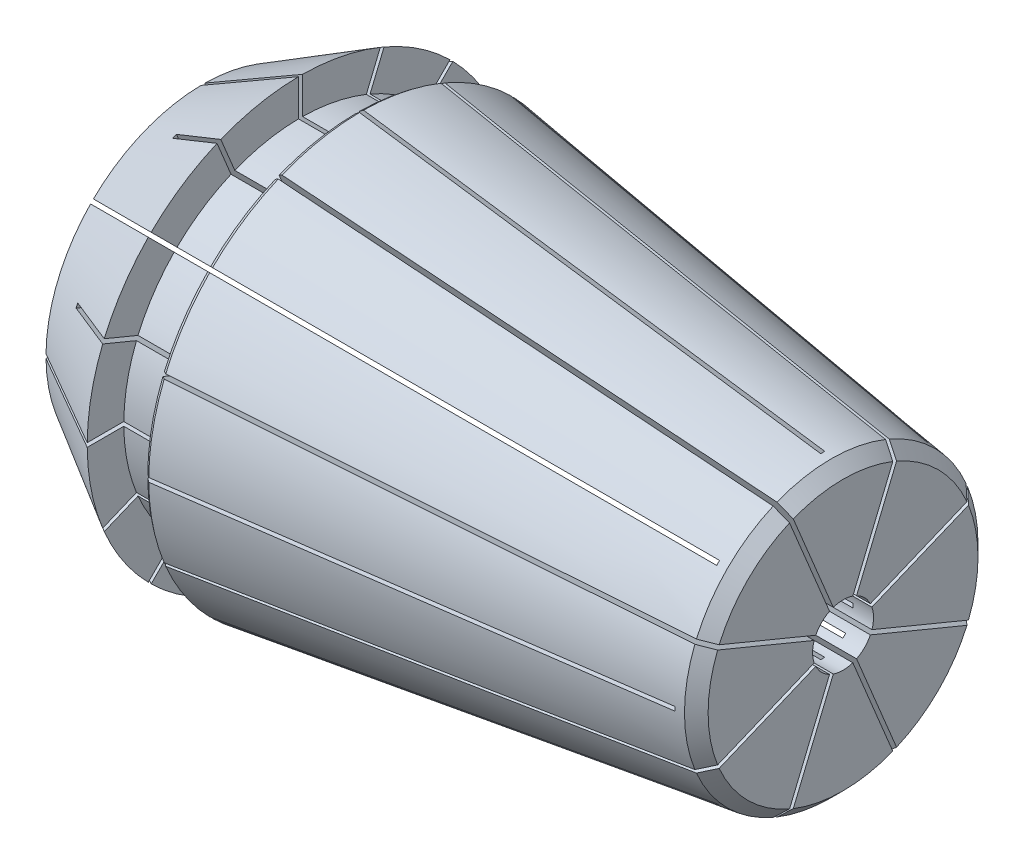
SolidWorks part; units mm, degrees
ref_plane "Front Plane" through (0, 0, 0) normal (0, 0, 1) x (1, 0, 0)
ref_plane "Top Plane" through (0, 0, 0) normal (0, 1, 0) x (1, 0, 0)
ref_plane "Right Plane" through (0, 0, 0) normal (1, 0, 0) x (0, 0, -1)
sketch "Sketch2" plane through (0, 0, 0) normal (1, 0, 0) x (0, 0, -1)
  circle A0 centre (0, 0) radius 10.5
  dimension "D1" = 21
extrude "Boss-Extrude1" add sketch "Sketch2" along normal blind 31.5
sketch "Sketch3" plane through (0, 0, 0) normal (0, 0, 1) x (1, 0, 0)
  line L0 (0, 0) -> (132.04, 0) construction
  line L1 (0, 7.7287) -> (4.8, 10.5)
  line L2 (0, 10.5) -> (0, -10.5) construction
  line L4 (4.8, 10.5) -> (4.8, 8.7)
  line L5 (4.8, 8.7) -> (7.6023, 8.7)
  line L6 (7.6023, 8.7) -> (7.6023, 10.5)
  line L7 (7.6023, 10.5) -> (31.5, 7.1414)
  line L8 (31.5, -10.5) -> (31.5, 10.5) construction
  line L9 (31.5, 7.1414) -> (31.5, 15.5)
  line L10 (31.5, 15.5) -> (0, 15.5)
  line L11 (0, 15.5) -> (0, 7.7287)
  line L13 (31.5, 10.5) -> (0, 10.5) construction
  line L15 (0, 0) -> (31.5, 0)
  line L16 (0, 0) -> (0, 1.5)
  line L17 (0, 1.5) -> (31.5, 1.5)
  line L18 (31.5, 0) -> (31.5, 1.5)
  point P9 (11.16, 10)
  dimension "D1" = 30
  dimension "D2" = 8
  dimension "D3" = 17.4
  dimension "D4" = 4.8
  dimension "D5" = 6.36
  dimension "D6" = 20
  dimension "D7" = 3
  dimension "D8" = 21
  dimension "D9" = 2.8023
  dimension "D10" = 5
revolve "Cut-Revolve1" cut sketch "Sketch3" angle 360 about L0
sketch "Sketch4" plane through (0, 0, 0) normal (-1, 0, 0) x (0, 0, 1)
  line L0 (21.8496, 21.991) -> (21.991, 21.8496)
  line L1 (-0.1, 31) -> (0.1, 31)
  line L2 (-0.1, 31) -> (-0.1, -31)
  line L3 (-0.1, -31) -> (0.1, -31)
  line L4 (0.1, 31) -> (0.1, -31)
  line L5 (-0.1, 31) -> (0.1, -31) construction
  line L6 (-0.1, -31) -> (0.1, 31) construction
  line L7 (21.8496, 21.991) -> (-21.991, -21.8496)
  line L8 (-21.991, -21.8496) -> (-21.8496, -21.991)
  line L9 (21.991, 21.8496) -> (-21.8496, -21.991)
  line L10 (21.8496, 21.991) -> (-21.8496, -21.991) construction
  line L11 (-21.991, -21.8496) -> (21.991, 21.8496) construction
  line L12 (31, 0.1) -> (31, -0.1)
  line L13 (31, 0.1) -> (-31, 0.1)
  line L14 (-31, 0.1) -> (-31, -0.1)
  line L15 (31, -0.1) -> (-31, -0.1)
  line L16 (31, 0.1) -> (-31, -0.1) construction
  line L17 (-31, 0.1) -> (31, -0.1) construction
  line L18 (21.991, -21.8496) -> (21.8496, -21.991)
  line L19 (21.991, -21.8496) -> (-21.8496, 21.991)
  line L20 (-21.8496, 21.991) -> (-21.991, 21.8496)
  line L21 (21.8496, -21.991) -> (-21.991, 21.8496)
  line L22 (21.991, -21.8496) -> (-21.991, 21.8496) construction
  line L23 (-21.8496, 21.991) -> (21.8496, -21.991) construction
  line L24 (0.1, -31) -> (-0.1, -31)
  line L25 (0.1, -31) -> (0.1, 31)
  line L26 (0.1, 31) -> (-0.1, 31)
  line L27 (-0.1, -31) -> (-0.1, 31)
  line L28 (0.1, -31) -> (-0.1, 31) construction
  line L29 (0.1, 31) -> (-0.1, -31) construction
  line L30 (-21.8496, -21.991) -> (-21.991, -21.8496)
  line L31 (-21.8496, -21.991) -> (21.991, 21.8496)
  line L32 (21.991, 21.8496) -> (21.8496, 21.991)
  line L33 (-21.991, -21.8496) -> (21.8496, 21.991)
  line L34 (-21.8496, -21.991) -> (21.8496, 21.991) construction
  line L35 (21.991, 21.8496) -> (-21.991, -21.8496) construction
  line L36 (-31, -0.1) -> (-31, 0.1)
  line L37 (-31, -0.1) -> (31, -0.1)
  line L38 (31, -0.1) -> (31, 0.1)
  line L39 (-31, 0.1) -> (31, 0.1)
  line L40 (-31, -0.1) -> (31, 0.1) construction
  line L41 (31, -0.1) -> (-31, 0.1) construction
  line L42 (-21.991, 21.8496) -> (-21.8496, 21.991)
  line L43 (-21.991, 21.8496) -> (21.8496, -21.991)
  line L44 (21.8496, -21.991) -> (21.991, -21.8496)
  line L45 (-21.8496, 21.991) -> (21.991, -21.8496)
  line L46 (-21.991, 21.8496) -> (21.991, -21.8496) construction
  line L47 (21.8496, -21.991) -> (-21.8496, 21.991) construction
  point P0 (0, 0)
  point P37 (0, 0)
  dimension "D3" = 31
  dimension "D1" = 0.2
  dimension "D2" = 8
extrude "Cut-Extrude1" cut sketch "Sketch4" against normal offset from surface (30.5 mm away) 1 contours L19 L20 L21 L18 | L13 L14 L15 L12 | L7 L8 L9 L0 | L4 L3 L2 L1 up to face at (31.5, 0, 1.5)
sketch "Sketch5" plane through (31.5, 0, 0) normal (1, 0, 0) x (0, 0, -1)
  line L0 (0, 0) -> (0, -5.7107) construction
  line L1 (-11.9556, -28.602) -> (-11.7708, -28.6785)
  line L2 (-11.9556, -28.602) -> (11.7708, 28.6785)
  line L3 (11.7708, 28.6785) -> (11.9556, 28.602)
  line L4 (-11.7708, -28.6785) -> (11.9556, 28.602)
  line L5 (-11.9556, -28.602) -> (11.9556, 28.602) construction
  line L6 (11.7708, 28.6785) -> (-11.7708, -28.6785) construction
  line L7 (28.602, 11.9556) -> (28.6785, 11.7708)
  line L8 (-28.602, -11.9556) -> (28.6785, 11.7708)
  line L9 (-28.6785, -11.7708) -> (28.602, 11.9556)
  line L10 (-28.6785, -11.7708) -> (-28.602, -11.9556)
  line L11 (28.6785, -11.7708) -> (28.602, -11.9556)
  line L12 (-28.6785, 11.7708) -> (28.602, -11.9556)
  line L13 (-28.602, 11.9556) -> (28.6785, -11.7708)
  line L14 (-28.602, 11.9556) -> (-28.6785, 11.7708)
  line L15 (11.9556, -28.602) -> (11.7708, -28.6785)
  line L16 (-11.9556, 28.602) -> (11.7708, -28.6785)
  line L17 (-11.7708, 28.6785) -> (11.9556, -28.602)
  line L18 (-11.7708, 28.6785) -> (-11.9556, 28.602)
  line L19 (-11.7708, -28.6785) -> (-11.9556, -28.602)
  line L20 (11.7708, 28.6785) -> (-11.9556, -28.602)
  line L21 (11.9556, 28.602) -> (-11.7708, -28.6785)
  line L22 (11.9556, 28.602) -> (11.7708, 28.6785)
  line L23 (-28.602, -11.9556) -> (-28.6785, -11.7708)
  line L24 (28.602, 11.9556) -> (-28.6785, -11.7708)
  line L25 (28.6785, 11.7708) -> (-28.602, -11.9556)
  line L26 (28.6785, 11.7708) -> (28.602, 11.9556)
  line L27 (-28.6785, 11.7708) -> (-28.602, 11.9556)
  line L28 (28.6785, -11.7708) -> (-28.602, 11.9556)
  line L29 (28.602, -11.9556) -> (-28.6785, 11.7708)
  line L30 (28.602, -11.9556) -> (28.6785, -11.7708)
  line L31 (-11.9556, 28.602) -> (-11.7708, 28.6785)
  line L32 (11.9556, -28.602) -> (-11.7708, 28.6785)
  line L33 (11.7708, -28.6785) -> (-11.9556, 28.602)
  line L34 (11.7708, -28.6785) -> (11.9556, -28.602)
  point P0 (0, 0)
  point P40 (0, 0)
  dimension "D1" = 0.2
  dimension "D2" = 22.5
  dimension "D3" = 8
extrude "Cut-Extrude2" cut sketch "Sketch5" against normal offset from surface (29.5 mm away) 2 contours L8 L7 L9 L10 | L12 L11 L13 L14 | L16 L15 L17 L18 | L4 L3 L2 L1 up to face at (0, 4.1177, 1.7056)
chamfer "Фаска1" distance 0.5 angle 45 8 edges at (0, -1.3858, -0.574) (0, -1.3858, 0.574) (0, -0.574, 1.3858) (0, 0.574, 1.3858) (0, 1.3858, 0.574) (0, 1.3858, -0.574) (0, 0.574, -1.3858) (0, -0.574, -1.3858)
chamfer "Фаска2" distance 0.2 angle 45 16 edges at (7.6023, 2.0484, 10.2982) (7.6023, 5.8335, 8.7304) (7.6023, 8.7304, 5.8335) (7.6023, -2.0484, 10.2982) (7.6023, -5.8335, 8.7304) (7.6023, -8.7304, 5.8335) (7.6023, -10.2982, 2.0484) (7.6023, -10.2982, -2.0484) (7.6023, -8.7304, -5.8335) (7.6023, -5.8335, -8.7304) (7.6023, -2.0484, -10.2982) (7.6023, 2.0484, -10.2982) (7.6023, 5.8335, -8.7304) (7.6023, 8.7304, -5.8335) (7.6023, 10.2982, -2.0484) (7.6023, 10.2982, 2.0484)
chamfer "Фаска3" distance 0.5 angle 45 8 edges at (31.5, -7.1414, 0) (31.5, -5.0497, -5.0497) (31.5, 0, -7.1414) (31.5, 5.0497, -5.0497) (31.5, 7.1414, 0) (31.5, 5.0497, 5.0497) (31.5, 0, 7.1414) (31.5, -5.0497, 5.0497)
equation "\"L\"= 13.5"
